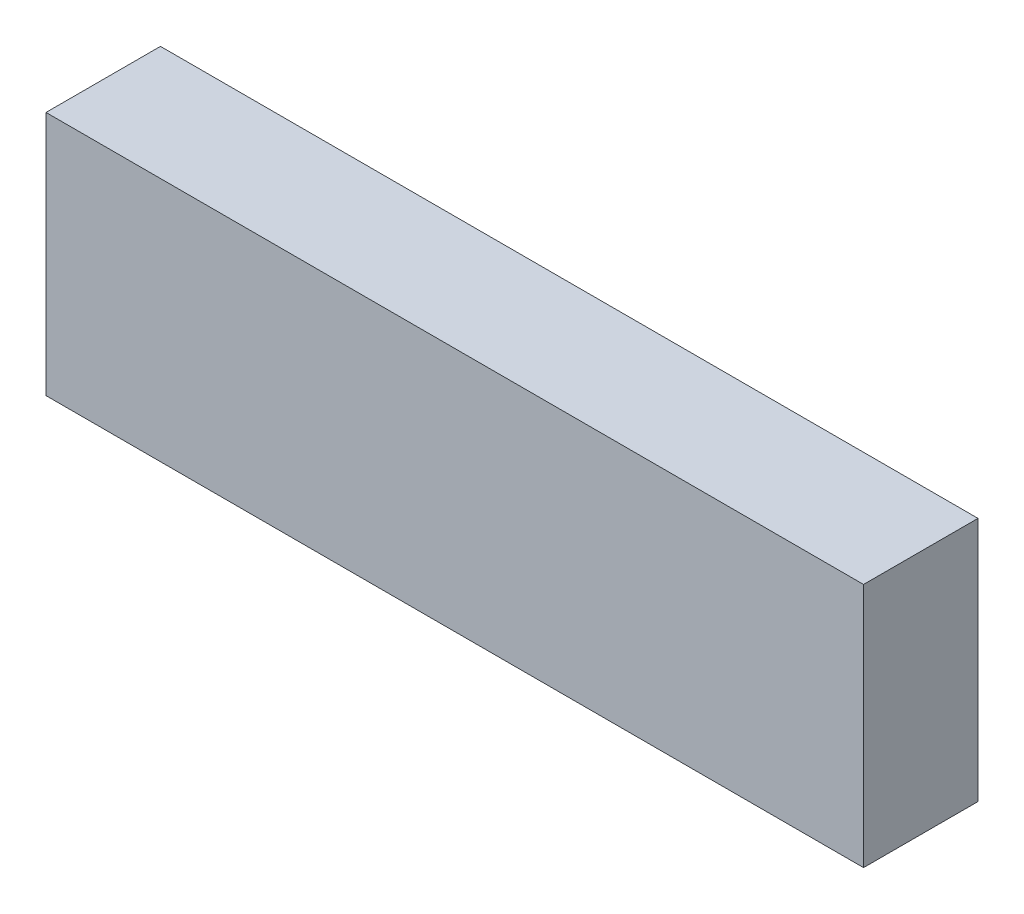
SolidWorks part; units mm, degrees
ref_plane "Front Plane" through (0, 0, 0) normal (0, 0, 1) x (1, 0, 0)
ref_plane "Top Plane" through (0, 0, 0) normal (0, 1, 0) x (1, 0, 0)
ref_plane "Right Plane" through (0, 0, 0) normal (1, 0, 0) x (0, 0, -1)
sketch "Sketch1" plane through (0, 0, 0) normal (0, 0, 1) x (1, 0, 0)
  line L1 (-65.3526, 22.3864) -> (61.6474, 22.3864)
  line L2 (-65.3526, 22.3864) -> (-65.3526, -15.7136)
  line L3 (-65.3526, -15.7136) -> (61.6474, -15.7136)
  line L4 (61.6474, 22.3864) -> (61.6474, -15.7136)
  dimension "D1" = 127
  dimension "D2" = 38.1
extrude "Boss-Extrude1" add sketch "Sketch1" along normal blind 17.78
